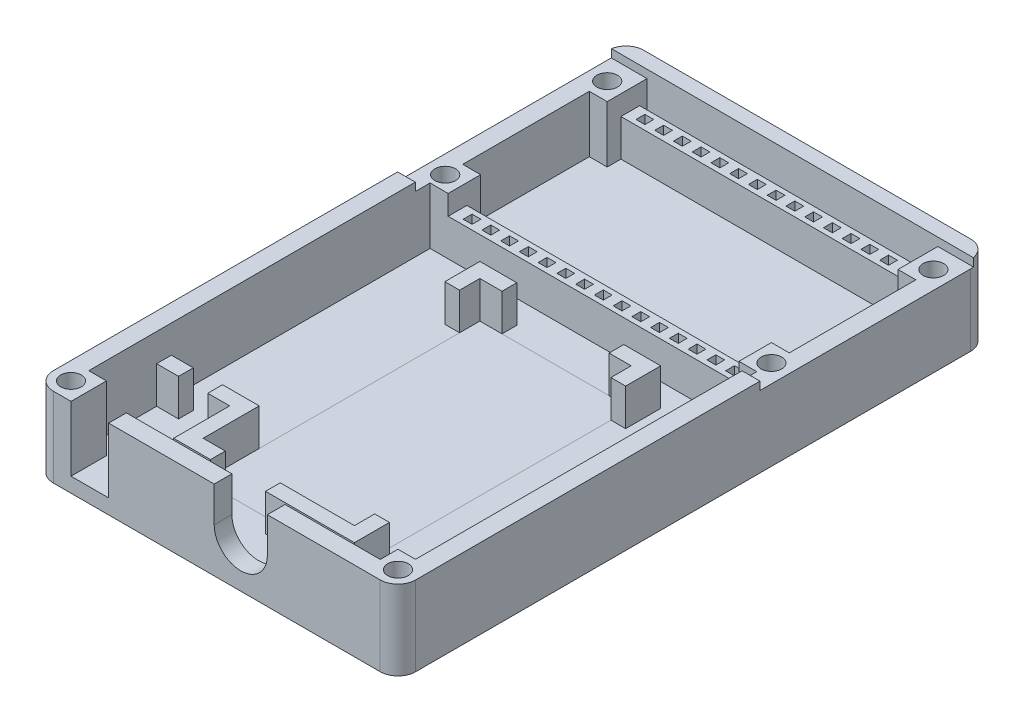
SolidWorks part; units mm, degrees
ref_plane "Front Plane" through (0, 0, 0) normal (0, 0, 1) x (1, 0, 0)
ref_plane "Top Plane" through (0, 0, 0) normal (0, 1, 0) x (1, 0, 0)
ref_plane "Right Plane" through (0, 0, 0) normal (1, 0, 0) x (0, 0, -1)
sketch "Sketch1" plane through (0, 0, 0) normal (0, 1, 0) x (1, 0, 0)
  line L1 (0, 0) -> (49.1, 0)
  line L2 (0, 0) -> (0, -80)
  line L3 (0, -80) -> (49.1, -80)
  line L4 (49.1, 0) -> (49.1, -80)
  dimension "D1" = 49.1
  dimension "D2" = 80
extrude "Boss-Extrude1" add sketch "Sketch1" along normal blind 2
sketch "Sketch2" plane through (0, 2, 0) normal (0, 1, 0) x (1, 0, 0)
  line L0 (24.55, 0) -> (24.55, -5) construction
  line L1 (2.45, -5) -> (46.65, -5) construction
  line L2 (2.45, -5) -> (2.45, -26.95) construction
  line L3 (2.45, -26.95) -> (46.65, -26.95) construction
  line L4 (46.65, -5) -> (46.65, -26.95) construction
  line L5 (49.1, 0) -> (0, 0) construction
  line L6 (0, 0) -> (0, -80) construction
  circle A0 centre (2.45, -5) radius 1.4
  circle A1 centre (46.65, -5) radius 1.4
  circle A2 centre (46.65, -26.95) radius 1.4
  circle A3 centre (2.45, -26.95) radius 1.4
  dimension "D3" = 2.8
  dimension "D1" = 44.2
  dimension "D2" = 21.95
  dimension "D4" = 5
  dimension "D5" = 2.45
extrude "Cut-Extrude1" cut sketch "Sketch2" against normal blind 2
sketch "Sketch3" plane through (0, 2, 0) normal (0, 1, 0) x (1, 0, 0)
  line L0 (2.45, -15.975) -> (46.65, -15.975) construction
  line L1 (2.45, -5) -> (46.65, -5) construction
  line L2 (2.45, -5) -> (2.45, -26.95) construction
  line L3 (2.45, -26.95) -> (46.65, -26.95) construction
  line L4 (46.65, -5) -> (46.65, -26.95) construction
  line L5 (6.22, -3.67) -> (7.42, -3.67)
  line L6 (6.22, -3.67) -> (6.22, -4.87)
  line L7 (6.22, -4.87) -> (7.42, -4.87)
  line L8 (7.42, -3.67) -> (7.42, -4.87)
  line L9 (5.55, -3) -> (8.09, -5.54) construction
  line L10 (5.55, -3) -> (8.09, -3) construction
  line L11 (5.55, -3) -> (5.55, -5.54) construction
  line L12 (5.55, -5.54) -> (8.09, -5.54) construction
  line L13 (8.09, -3) -> (8.09, -5.54) construction
  line L14 (8.09, -3) -> (5.55, -5.54) construction
  line L15 (6.22, -3.67) -> (7.42, -4.87) construction
  line L16 (8.76, -3.67) -> (9.96, -3.67)
  line L17 (8.76, -3.67) -> (8.76, -4.87)
  line L18 (9.96, -3.67) -> (9.96, -4.87)
  line L19 (8.76, -4.87) -> (9.96, -4.87)
  line L20 (11.3, -3.67) -> (12.5, -3.67)
  line L21 (11.3, -3.67) -> (11.3, -4.87)
  line L22 (12.5, -3.67) -> (12.5, -4.87)
  line L23 (11.3, -4.87) -> (12.5, -4.87)
  line L24 (13.84, -3.67) -> (15.04, -3.67)
  line L25 (13.84, -3.67) -> (13.84, -4.87)
  line L26 (15.04, -3.67) -> (15.04, -4.87)
  line L27 (13.84, -4.87) -> (15.04, -4.87)
  line L28 (16.38, -3.67) -> (17.58, -3.67)
  line L29 (16.38, -3.67) -> (16.38, -4.87)
  line L30 (17.58, -3.67) -> (17.58, -4.87)
  line L31 (16.38, -4.87) -> (17.58, -4.87)
  line L32 (18.92, -3.67) -> (20.12, -3.67)
  line L33 (18.92, -3.67) -> (18.92, -4.87)
  line L34 (20.12, -3.67) -> (20.12, -4.87)
  line L35 (18.92, -4.87) -> (20.12, -4.87)
  line L36 (21.46, -3.67) -> (22.66, -3.67)
  line L37 (21.46, -3.67) -> (21.46, -4.87)
  line L38 (22.66, -3.67) -> (22.66, -4.87)
  line L39 (21.46, -4.87) -> (22.66, -4.87)
  line L40 (24, -3.67) -> (25.2, -3.67)
  line L41 (24, -3.67) -> (24, -4.87)
  line L42 (25.2, -3.67) -> (25.2, -4.87)
  line L43 (24, -4.87) -> (25.2, -4.87)
  line L44 (26.54, -3.67) -> (27.74, -3.67)
  line L45 (26.54, -3.67) -> (26.54, -4.87)
  line L46 (27.74, -3.67) -> (27.74, -4.87)
  line L47 (26.54, -4.87) -> (27.74, -4.87)
  line L48 (29.08, -3.67) -> (30.28, -3.67)
  line L49 (29.08, -3.67) -> (29.08, -4.87)
  line L50 (30.28, -3.67) -> (30.28, -4.87)
  line L51 (29.08, -4.87) -> (30.28, -4.87)
  line L52 (31.62, -3.67) -> (32.82, -3.67)
  line L53 (31.62, -3.67) -> (31.62, -4.87)
  line L54 (32.82, -3.67) -> (32.82, -4.87)
  line L55 (31.62, -4.87) -> (32.82, -4.87)
  line L56 (34.16, -3.67) -> (35.36, -3.67)
  line L57 (34.16, -3.67) -> (34.16, -4.87)
  line L58 (35.36, -3.67) -> (35.36, -4.87)
  line L59 (34.16, -4.87) -> (35.36, -4.87)
  line L60 (36.7, -3.67) -> (37.9, -3.67)
  line L61 (36.7, -3.67) -> (36.7, -4.87)
  line L62 (37.9, -3.67) -> (37.9, -4.87)
  line L63 (36.7, -4.87) -> (37.9, -4.87)
  line L64 (39.24, -3.67) -> (40.44, -3.67)
  line L65 (39.24, -3.67) -> (39.24, -4.87)
  line L66 (40.44, -3.67) -> (40.44, -4.87)
  line L67 (39.24, -4.87) -> (40.44, -4.87)
  line L68 (41.78, -3.67) -> (42.98, -3.67)
  line L69 (41.78, -3.67) -> (41.78, -4.87)
  line L70 (42.98, -3.67) -> (42.98, -4.87)
  line L71 (41.78, -4.87) -> (42.98, -4.87)
  line L72 (6.22, -28.28) -> (7.42, -27.08) construction
  line L73 (8.09, -28.95) -> (5.55, -26.41) construction
  line L74 (8.09, -28.95) -> (8.09, -26.41) construction
  line L75 (5.55, -26.41) -> (8.09, -26.41) construction
  line L76 (5.55, -28.95) -> (5.55, -26.41) construction
  line L77 (5.55, -28.95) -> (8.09, -28.95) construction
  line L78 (5.55, -28.95) -> (8.09, -26.41) construction
  line L79 (2.45, -26.95) -> (46.65, -26.95) construction
  line L80 (41.78, -27.08) -> (42.98, -27.08)
  line L81 (42.98, -28.28) -> (42.98, -27.08)
  line L82 (41.78, -28.28) -> (41.78, -27.08)
  line L83 (41.78, -28.28) -> (42.98, -28.28)
  line L84 (39.24, -27.08) -> (40.44, -27.08)
  line L85 (40.44, -28.28) -> (40.44, -27.08)
  line L86 (39.24, -28.28) -> (39.24, -27.08)
  line L87 (39.24, -28.28) -> (40.44, -28.28)
  line L88 (36.7, -27.08) -> (37.9, -27.08)
  line L89 (37.9, -28.28) -> (37.9, -27.08)
  line L90 (36.7, -28.28) -> (36.7, -27.08)
  line L91 (36.7, -28.28) -> (37.9, -28.28)
  line L92 (34.16, -27.08) -> (35.36, -27.08)
  line L93 (35.36, -28.28) -> (35.36, -27.08)
  line L94 (34.16, -28.28) -> (34.16, -27.08)
  line L95 (34.16, -28.28) -> (35.36, -28.28)
  line L96 (31.62, -27.08) -> (32.82, -27.08)
  line L97 (32.82, -28.28) -> (32.82, -27.08)
  line L98 (31.62, -28.28) -> (31.62, -27.08)
  line L99 (31.62, -28.28) -> (32.82, -28.28)
  line L100 (29.08, -27.08) -> (30.28, -27.08)
  line L101 (30.28, -28.28) -> (30.28, -27.08)
  line L102 (29.08, -28.28) -> (29.08, -27.08)
  line L103 (29.08, -28.28) -> (30.28, -28.28)
  line L104 (26.54, -27.08) -> (27.74, -27.08)
  line L105 (27.74, -28.28) -> (27.74, -27.08)
  line L106 (26.54, -28.28) -> (26.54, -27.08)
  line L107 (26.54, -28.28) -> (27.74, -28.28)
  line L108 (24, -27.08) -> (25.2, -27.08)
  line L109 (25.2, -28.28) -> (25.2, -27.08)
  line L110 (24, -28.28) -> (24, -27.08)
  line L111 (24, -28.28) -> (25.2, -28.28)
  line L112 (21.46, -27.08) -> (22.66, -27.08)
  line L113 (22.66, -28.28) -> (22.66, -27.08)
  line L114 (21.46, -28.28) -> (21.46, -27.08)
  line L115 (21.46, -28.28) -> (22.66, -28.28)
  line L116 (18.92, -27.08) -> (20.12, -27.08)
  line L117 (20.12, -28.28) -> (20.12, -27.08)
  line L118 (18.92, -28.28) -> (18.92, -27.08)
  line L119 (18.92, -28.28) -> (20.12, -28.28)
  line L120 (16.38, -27.08) -> (17.58, -27.08)
  line L121 (17.58, -28.28) -> (17.58, -27.08)
  line L122 (16.38, -28.28) -> (16.38, -27.08)
  line L123 (16.38, -28.28) -> (17.58, -28.28)
  line L124 (13.84, -27.08) -> (15.04, -27.08)
  line L125 (15.04, -28.28) -> (15.04, -27.08)
  line L126 (13.84, -28.28) -> (13.84, -27.08)
  line L127 (13.84, -28.28) -> (15.04, -28.28)
  line L128 (11.3, -27.08) -> (12.5, -27.08)
  line L129 (12.5, -28.28) -> (12.5, -27.08)
  line L130 (11.3, -28.28) -> (11.3, -27.08)
  line L131 (11.3, -28.28) -> (12.5, -28.28)
  line L132 (8.76, -27.08) -> (9.96, -27.08)
  line L133 (9.96, -28.28) -> (9.96, -27.08)
  line L134 (8.76, -28.28) -> (8.76, -27.08)
  line L135 (8.76, -28.28) -> (9.96, -28.28)
  line L136 (7.42, -28.28) -> (7.42, -27.08)
  line L137 (6.22, -27.08) -> (7.42, -27.08)
  line L138 (6.22, -28.28) -> (6.22, -27.08)
  line L139 (6.22, -28.28) -> (7.42, -28.28)
  line L140 (0, 0) -> (0, -80) construction
  line L141 (4.85, -3) -> (44.25, -3)
  line L142 (0, -3) -> (0, -28.95)
  line L143 (0, -28.95) -> (49.1, -28.95)
  line L144 (49.1, -3) -> (49.1, -28.95)
  line L145 (49.1, -80) -> (49.1, 0) construction
  line L146 (24.55, -15.975) -> (24.55, -7.9718) construction
  line L148 (4.85, -3) -> (4.85, -2.6)
  line L149 (4.85, -2.6) -> (0, -2.6)
  line L150 (0, -3) -> (0, -2.6)
  line L151 (44.25, -2.6) -> (49.1, -2.6)
  line L152 (49.1, -3) -> (49.1, -2.6)
  line L154 (44.25, -3) -> (44.25, -2.6)
  circle A0 centre (2.45, -5) radius 1.4 construction
  circle A1 centre (2.45, -5) radius 1.4
  circle A2 centre (2.45, -26.95) radius 1.4
  circle A3 centre (46.65, -5) radius 1.4
  circle A4 centre (46.65, -26.95) radius 1.4
  circle A5 centre (2.45, -26.95) radius 1.4 construction
  point P12 (6.82, -4.27)
  point P139 (6.82, -27.68)
  dimension "D5" = 2
  dimension "D6" = 3.1
  dimension "D1" = 1.2
  dimension "D2" = 1.2
  dimension "D3" = 2.54
  dimension "D4" = 2.54
  dimension "D8" = 2.54
  dimension "D9" = 2.4
  dimension "D10" = 2.4
  dimension "D7" = 15
extrude "Boss-Extrude2" add sketch "Sketch3" along normal blind 5
sketch "Sketch4" plane through (0, 7, 0) normal (0, 1, 0) x (1, 0, 0)
  line L0 (0, -15.975) -> (49.1, -15.975) construction
  line L1 (0, -2.6) -> (0, -28.95) construction
  line L2 (49.1, -2.6) -> (44.25, -2.6) construction
  line L3 (24.55, -3) -> (24.55, -28.95) construction
  line L4 (44.25, -3) -> (4.85, -3) construction
  line L5 (0, -28.95) -> (49.1, -28.95) construction
  line L6 (0, -28.95) -> (49.1, -28.95) construction
  line L7 (0, -24.55) -> (4.85, -24.55)
  line L8 (0, -24.55) -> (0, -28.95)
  line L9 (0, -28.95) -> (4.85, -28.95)
  line L10 (4.85, -24.55) -> (4.85, -28.95)
  line L11 (49.1, -28.95) -> (44.25, -28.95)
  line L12 (44.25, -24.55) -> (44.25, -28.95)
  line L13 (49.1, -24.55) -> (44.25, -24.55)
  line L14 (49.1, -24.55) -> (49.1, -28.95)
  line L15 (49.1, -7.4) -> (49.1, -3)
  line L16 (49.1, -7.4) -> (44.25, -7.4)
  line L17 (44.25, -7.4) -> (44.25, -3)
  line L20 (4.85, -7.4) -> (4.85, -3)
  line L21 (0, -7.4) -> (4.85, -7.4)
  line L22 (0, -7.4) -> (0, -3)
  line L23 (44.25, -2.6) -> (49.1, -2.6)
  line L24 (0, -2.6) -> (4.85, -2.6)
  line L25 (0, -2.6) -> (0, -3)
  line L27 (4.85, -2.6) -> (4.85, -3)
  line L28 (44.25, -2.6) -> (44.25, -3)
  line L30 (49.1, -2.6) -> (49.1, -3)
  line L31 (49.1, -2.6) -> (49.1, 0) construction
  circle A0 centre (2.45, -5) radius 1.4 construction
  circle A1 centre (2.45, -26.95) radius 1.4
  circle A2 centre (2.45, -26.95) radius 1.4 construction
  circle A3 centre (46.65, -26.95) radius 1.4
  circle A4 centre (2.45, -5) radius 1.4
  circle A5 centre (46.65, -5) radius 1.4
  dimension "D1" = 2.4
  dimension "D2" = 2.4
extrude "Boss-Extrude3" add sketch "Sketch4" along normal blind 2.68
sketch "Sketch5" plane through (0, 2, 0) normal (0, 1, 0) x (1, 0, 0)
  line L0 (0, -52.85) -> (49.1, -52.85) construction
  line L1 (0, -80) -> (49.1, -80) construction
  line L3 (0, -28.95) -> (49.1, -28.95) construction
  line L4 (14.3, -34.1) -> (34.8, -34.1)
  line L5 (14.3, -34.1) -> (14.3, -71.6)
  line L6 (14.3, -71.6) -> (34.8, -71.6)
  line L7 (34.8, -34.1) -> (34.8, -71.6)
  line L8 (14.3, -34.1) -> (34.8, -71.6) construction
  line L9 (14.3, -71.6) -> (34.8, -34.1) construction
  line L10 (12.3, -68.85) -> (17.3, -68.85)
  line L11 (12.3, -32.1) -> (36.8, -32.1)
  line L12 (12.3, -32.1) -> (12.3, -73.6)
  line L13 (12.3, -73.6) -> (36.8, -73.6)
  line L14 (36.8, -32.1) -> (36.8, -73.6)
  line L15 (12.3, -32.1) -> (36.8, -73.6) construction
  line L16 (12.3, -73.6) -> (36.8, -32.1) construction
  line L17 (12.3, -32.1) -> (17.3, -32.1)
  line L18 (12.3, -32.1) -> (12.3, -36.85)
  line L19 (12.3, -36.85) -> (17.3, -36.85)
  line L20 (17.3, -32.1) -> (17.3, -36.85)
  line L21 (17.3, -73.6) -> (17.3, -68.85)
  line L22 (12.3, -73.6) -> (17.3, -73.6)
  line L23 (12.3, -73.6) -> (12.3, -68.85)
  line L24 (24.55, -52.85) -> (24.55, -28.95) construction
  line L25 (36.8, -36.85) -> (31.8, -36.85)
  line L26 (31.8, -32.1) -> (31.8, -36.85)
  line L27 (36.8, -32.1) -> (31.8, -32.1)
  line L28 (36.8, -32.1) -> (36.8, -36.85)
  line L29 (36.8, -73.6) -> (31.8, -73.6)
  line L30 (31.8, -73.6) -> (31.8, -68.85)
  line L31 (36.8, -68.85) -> (31.8, -68.85)
  line L32 (36.8, -73.6) -> (36.8, -68.85)
  line L33 (24.7526, -71.6) -> (24.7526, -73.6)
  line L34 (32.7526, -71.6) -> (32.7526, -73.6)
  line L35 (0, -28.95) -> (0, -80) construction
  point P6 (24.55, -52.85)
  point P13 (24.55, -52.85)
  dimension "D1" = 37.5
  dimension "D2" = 20.5
  dimension "D3" = 6.4
  dimension "D4" = 2
  dimension "D5" = 2
  dimension "D6" = 2.75
  dimension "D7" = 3
  dimension "D8" = 8
extrude "Boss-Extrude4" add sketch "Sketch5" along normal blind 5 contours L20 L11 L12 L19 L5 L4 | L11 L26 L4 L7 L25 L14 | L6 L34 L29 L14 L31 L7 | L13 L21 L6 L5 L10 L12 | L6 L33 L13 L30 | L34 L6 L30 L13
sketch "Sketch6" plane through (0, 2, 0) normal (0, 1, 0) x (1, 0, 0)
  line L0 (0, -28.95) -> (0, -80) construction
  line L1 (0, -75.2) -> (4.8, -75.2)
  line L2 (0, -75.2) -> (0, -80)
  line L3 (0, -80) -> (4.8, -80)
  line L4 (4.8, -75.2) -> (4.8, -80)
  line L5 (0, -80) -> (49.1, -80) construction
  line L6 (24.55, -80) -> (24.55, -43.6832) construction
  line L7 (0, -80) -> (4.8, -75.2) construction
  line L8 (49.1, -80) -> (44.3, -75.2) construction
  line L9 (44.3, -75.2) -> (44.3, -80)
  line L10 (49.1, -80) -> (44.3, -80)
  line L11 (49.1, -75.2) -> (49.1, -80)
  line L12 (49.1, -75.2) -> (44.3, -75.2)
  circle A0 centre (2.4, -77.6) radius 1.4
  circle A1 centre (46.7, -77.6) radius 1.4
  dimension "D1" = 2.8
  dimension "D3" = 2.4
  dimension "D2" = 2.4
extrude "Boss-Extrude5" add sketch "Sketch6" along normal blind 8.78
sketch "Sketch7" plane through (0, 2, 0) normal (0, 1, 0) x (1, 0, 0)
  line L0 (4.8, -75.2) -> (0, -75.2) construction
  line L1 (0, -28.95) -> (2.4, -28.95)
  line L2 (0, -28.95) -> (0, -75.2)
  line L3 (0, -75.2) -> (2.4, -75.2)
  line L4 (2.4, -28.95) -> (2.4, -75.2)
  line L5 (44.25, -28.95) -> (49.1, -28.95) construction
  line L6 (49.1, -75.2) -> (46.675, -75.2)
  line L7 (49.1, -75.2) -> (49.1, -28.95)
  line L8 (49.1, -28.95) -> (46.675, -28.95)
  line L9 (46.675, -75.2) -> (46.675, -28.95)
  line L10 (49.1, -2.6) -> (49.1, 0) construction
  line L11 (0, 0) -> (49.1, 0)
  line L12 (0, 0) -> (0, -2)
  line L13 (4.85, -2) -> (44.25, -2)
  line L14 (49.1, 0) -> (49.1, -2)
  line L15 (44.25, -3) -> (4.85, -3) construction
  line L16 (4.8, -80) -> (4.8, -75.2) construction
  line L17 (4.8, -77.6) -> (44.3, -77.6)
  line L18 (4.8, -77.6) -> (4.8, -80)
  line L19 (4.8, -80) -> (44.3, -80)
  line L20 (44.3, -77.6) -> (44.3, -80)
  line L23 (0, -2) -> (0, -2.6)
  line L24 (0, -2.6) -> (4.85, -2.6)
  line L25 (4.85, -2) -> (4.85, -2.6)
  line L26 (49.1, -2.6) -> (44.25, -2.6)
  line L27 (49.1, -2.6) -> (49.1, -2)
  line L29 (44.25, -2.6) -> (44.25, -2)
  line L31 (4.85, -7.4) -> (4.85, -2.6) construction
  line L32 (44.25, -3) -> (44.25, -7.4) construction
  dimension "D1" = 2
  dimension "D2" = 2
  dimension "D3" = 0.4
  dimension "D4" = 0.4
extrude "Boss-Extrude6" add sketch "Sketch7" along normal up to surface (8.78 mm away) up to face at (2.4, 10.78, 77.6)
sketch "Sketch8" plane through (0, 0, 80) normal (0, 0, 1) x (1, 0, 0)
  line L0 (0, 0) -> (49.1, 0) construction
  line L2 (4.8, 8.2) -> (4.8, 2)
  line L3 (4.8, 2) -> (9.9, 2)
  line L4 (9.9, 8.2) -> (9.9, 2)
  line L6 (23, 10) -> (32.6, 10) construction
  line L7 (23, 10) -> (23, 2) construction
  line L8 (23, 2) -> (32.6, 2) construction
  line L9 (32.6, 10) -> (32.6, 2) construction
  line L10 (27.8, 10) -> (27.8, 2) construction
  line L11 (0, 10.78) -> (0, 0) construction
  line L12 (24.2, 6) -> (24.2, 10.78)
  line L13 (0, 10.78) -> (49.1, 10.78) construction
  line L14 (24.2, 10.78) -> (31.4, 10.78)
  line L15 (31.4, 10.78) -> (31.4, 6)
  line L16 (49.1, 10.78) -> (49.1, 0) construction
  line L18 (4.8, 8.2) -> (4.8, 10.78)
  line L19 (4.8, 10.78) -> (9.9, 10.78)
  line L20 (9.9, 8.2) -> (9.9, 10.78)
  line L21 (7.35, 2) -> (7.35, 10.78) construction
  arc A0 (24.2, 6) -> (31.4, 6) centre (27.8, 6) ccw
  dimension "D6" = 7.2
  dimension "D1" = 6.2
  dimension "D2" = 21.3
  dimension "D3" = 2
  dimension "D4" = 4.8
  dimension "D5" = 8
  dimension "D7" = 9.6
  dimension "D8" = 7.35
  dimension "D10" = 5.1
extrude "Cut-Extrude2" cut sketch "Sketch8" against normal blind 2.4
sketch "Sketch11" plane through (0, 2, 0) normal (0, 1, 0) x (1, 0, 0)
  circle A0 centre (2.4, -77.6) radius 1.4
  circle A1 centre (2.4, -77.6) radius 1.4 construction
  circle A2 centre (46.7, -77.6) radius 1.4
  circle A3 centre (46.7, -77.6) radius 1.4 construction
extrude "Cut-Extrude4" cut sketch "Sketch11" against normal blind 2
sketch "Sketch12" plane through (0, 2, 0) normal (0, 1, 0) x (1, 0, 0)
  line L1 (14.3, -34.1) -> (34.8, -34.1)
  line L2 (14.3, -34.1) -> (14.3, -71.6)
  line L3 (14.3, -71.6) -> (34.8, -71.6)
  line L4 (34.8, -34.1) -> (34.8, -71.6)
split line "Split Line1"
sketch "Sketch13" plane through (0, 2, 0) normal (0, 1, 0) x (1, 0, 0)
  line L1 (12.3, -66) -> (9.33, -66)
  line L2 (14.3, -66) -> (14.3, -64)
  line L3 (14.3, -64) -> (9.33, -64)
  line L4 (9.33, -66) -> (9.33, -64)
  line L6 (2.4, -75.2) -> (2.4, -28.95) construction
  line L7 (5.37, -64) -> (2.4, -64)
  line L8 (5.37, -64) -> (5.37, -66)
  line L9 (5.37, -66) -> (2.4, -66)
  line L10 (2.4, -64) -> (2.4, -66)
  line L11 (4.8, -80) -> (4.8, -75.2) construction
  line L12 (6.07, -80) -> (6.07, -62.0456) construction
  line L13 (4.8, -80) -> (9.9, -80) construction
  line L14 (8.63, -80) -> (8.63, -61.6074) construction
  line L15 (9.9, -77.6) -> (9.9, -80) construction
  line L16 (9.9, -80) -> (24.2, -80) construction
  line L17 (14.3, -68.85) -> (14.3, -71.6) construction
  line L20 (14.3, -66) -> (14.3, -68.85)
  line L21 (14.3, -68.85) -> (12.3, -68.85)
  line L22 (12.3, -66) -> (12.3, -68.85)
  dimension "D1" = 0.7
  dimension "D2" = 14
  dimension "D3" = 2
  dimension "D4" = 0.7
  dimension "D5" = 1.27
  dimension "D6" = 1.27
extrude "Boss-Extrude7" add sketch "Sketch13" along normal blind 5
sketch "Sketch14" plane through (0, 7, 0) normal (0, 1, 0) x (1, 0, 0)
  line L0 (49.1, -24.55) -> (44.25, -24.55) construction
  line L1 (49.1, -7.4) -> (46.675, -7.4)
  line L2 (49.1, -7.4) -> (49.1, -24.55)
  line L3 (49.1, -24.55) -> (46.675, -24.55)
  line L4 (46.675, -7.4) -> (46.675, -24.55)
  line L5 (4.85, -24.55) -> (0, -24.55) construction
  line L6 (0, -7.4) -> (2.425, -7.4)
  line L7 (0, -7.4) -> (0, -24.55)
  line L8 (0, -24.55) -> (2.425, -24.55)
  line L9 (2.425, -7.4) -> (2.425, -24.55)
extrude "Boss-Extrude8" add sketch "Sketch14" along normal up to surface (2.68 mm away) up to face at (46.675, 9.68, 27.19)
sketch "Sketch16" plane through (0, 7, 0) normal (0, 1, 0) x (1, 0, 0)
  line L0 (4.85, -5.54) -> (44.25, -5.54) construction
  line L1 (4.85, -7.4) -> (4.85, -3) construction
  line L2 (44.25, -3) -> (44.25, -7.4) construction
  line L3 (44.25, -3) -> (4.85, -3) construction
  line L4 (4.85, -26.41) -> (44.25, -26.41) construction
  line L5 (4.85, -28.95) -> (4.85, -24.55) construction
  line L6 (44.25, -24.55) -> (44.25, -28.95) construction
  line L7 (4.85, -28.95) -> (44.25, -28.95) construction
  line L8 (4.85, -24.55) -> (4.85, -26.41)
  line L9 (4.85, -5.54) -> (44.25, -5.54)
  line L10 (4.85, -5.54) -> (4.85, -7.4)
  line L11 (4.85, -26.41) -> (44.25, -26.41)
  line L12 (44.25, -5.54) -> (44.25, -7.4)
  line L13 (2.425, -7.4) -> (4.85, -7.4)
  line L14 (2.425, -7.4) -> (2.425, -24.55)
  line L15 (2.425, -24.55) -> (4.85, -24.55)
  line L17 (46.675, -7.4) -> (44.25, -7.4)
  line L18 (46.675, -7.4) -> (46.675, -24.55)
  line L19 (46.675, -24.55) -> (44.25, -24.55)
  line L21 (44.25, -24.55) -> (44.25, -26.41)
  dimension "D1" = 2.54
  dimension "D2" = 2.54
extrude "Cut-Extrude5" cut sketch "Sketch16" against normal offset from surface (5 mm away) 2 up to face at (2.4, 0, 79)
sketch "Sketch17" plane through (0, 10.78, 0) normal (0, 1, 0) x (1, 0, 0)
  line L0 (2.4, -75.2) -> (2.4, -28.95) construction
  line L1 (0, -2.6) -> (4.85, -2.6)
  line L2 (0, -2.6) -> (0, -2)
  line L3 (0, -2) -> (4.85, -2)
  line L4 (4.85, -2.6) -> (4.85, -2)
  line L5 (49.1, -2.6) -> (44.25, -2.6)
  line L6 (49.1, -2.6) -> (49.1, -2)
  line L7 (49.1, -2) -> (44.25, -2)
  line L8 (44.25, -2.6) -> (44.25, -2)
  line L9 (0, -28.95) -> (2.4, -28.95)
  line L10 (0, -28.95) -> (0, -30.95)
  line L11 (0, -30.95) -> (2.4, -30.95)
  line L12 (2.4, -28.95) -> (2.4, -30.95)
  line L13 (49.1, -80) -> (49.1, -28.95) construction
  line L14 (46.675, -28.95) -> (49.1, -28.95)
  line L15 (46.675, -28.95) -> (46.675, -30.95)
  line L16 (46.675, -30.95) -> (49.1, -30.95)
  line L17 (49.1, -28.95) -> (49.1, -30.95)
  dimension "D1" = 2
extrude "Cut-Extrude6" cut sketch "Sketch17" against normal up to surface (1.1 mm away) up to face at (2.9611, 9.68, 17.3278)
fillet "Fillet1" radius 2.4 4 edges at (0, 5.39, 80) (49.1, 5.39, 80) (49.1, 5.39, 0) (0, 5.39, 0)
